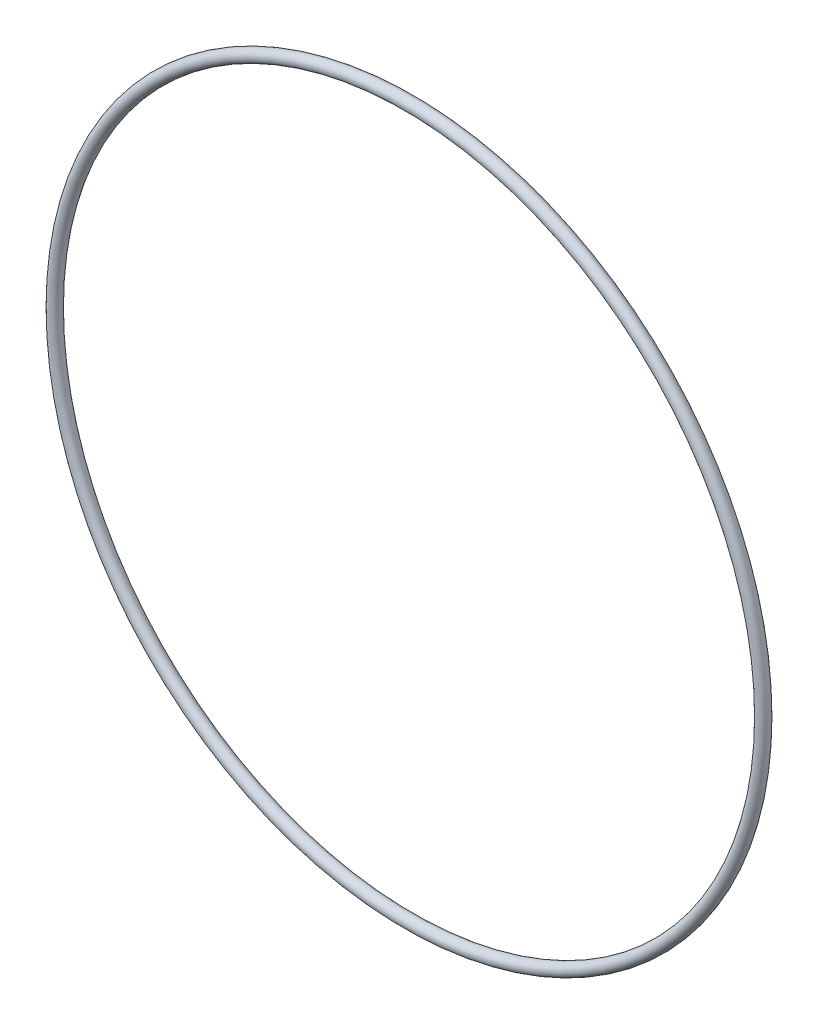
SolidWorks part; units mm, degrees
material "NBR"
ref_plane "前基準面" through (0, 0, 0) normal (0, 0, 1) x (1, 0, 0)
ref_plane "上基準面" through (0, 0, 0) normal (0, 1, 0) x (1, 0, 0)
ref_plane "右基準面" through (0, 0, 0) normal (1, 0, 0) x (0, 0, -1)
sketch "Sketch1" plane through (0, 0, 0) normal (0, 0, 1) x (1, 0, 0)
  circle A0 centre (0, 0) radius 85
  dimension "D1" = 170
sketch "Sketch2" plane through (0, 0, 0) normal (0, 1, 0) x (1, 0, 0)
  circle A0 centre (-86.5, 0) radius 1.5
  dimension "D1" = 3
  dimension "D2" = 86.5
ref_axis "Axis2" through (0, 0, -1.65) along (0, 0, 1)
revolve "Revolve1" add sketch "Sketch2" angle 360 about axis through (0, 0, -1.65) along (0, 0, 1)
